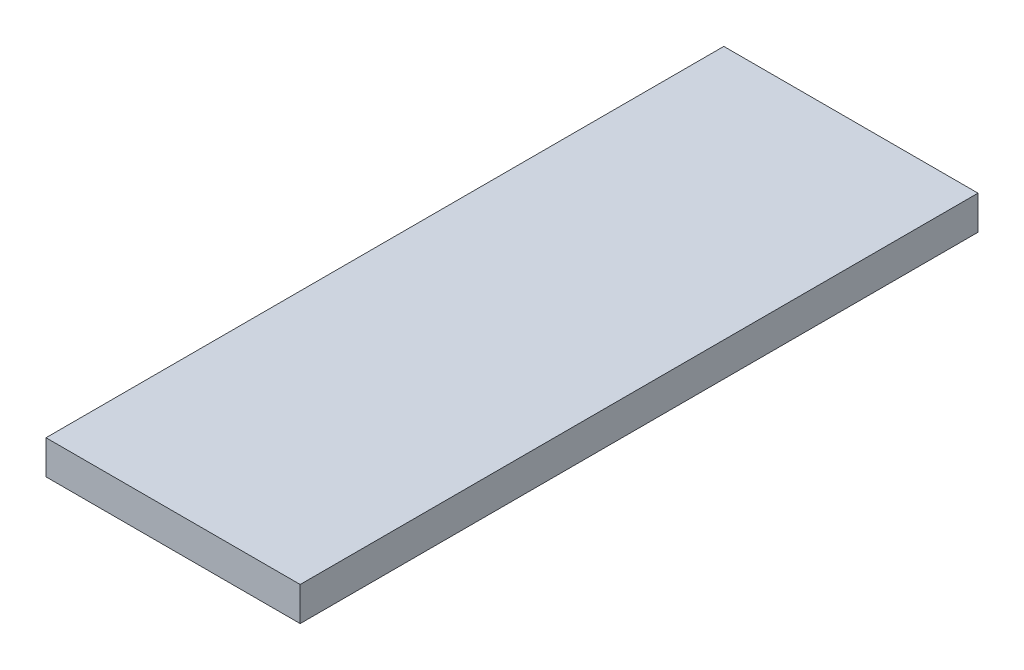
SolidWorks part; units mm, degrees
material "Oak"
ref_plane "Front Plane" through (0, 0, 0) normal (0, 0, 1) x (1, 0, 0)
ref_plane "Top Plane" through (0, 0, 0) normal (0, 1, 0) x (1, 0, 0)
ref_plane "Right Plane" through (0, 0, 0) normal (1, 0, 0) x (0, 0, -1)
sketch "Sketch1" plane through (0, 0, 0) normal (0, 1, 0) x (1, 0, 0)
  line L1 (-75, 200) -> (75, 200)
  line L2 (-75, 200) -> (-75, -200)
  line L3 (-75, -200) -> (75, -200)
  line L4 (75, 200) -> (75, -200)
  line L5 (-75, 200) -> (75, -200) construction
  line L6 (-75, -200) -> (75, 200) construction
  point P0 (0, 0)
  dimension "D1" = 400
  dimension "D2" = 150
extrude "Boss-Extrude1" add sketch "Sketch1" along normal blind 20
